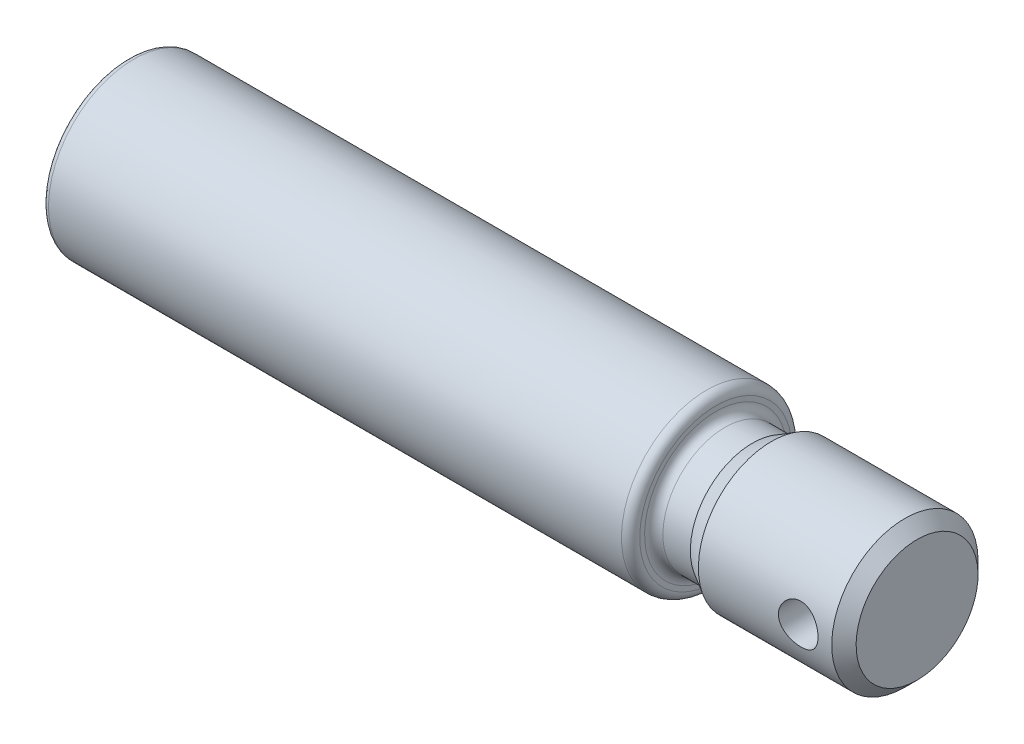
SolidWorks part; units mm, degrees
ref_plane "Plane1" through (0, 0, 0) normal (0, 0, 1) x (1, 0, 0)
ref_plane "Plane2" through (0, 0, 0) normal (0, 1, 0) x (1, 0, 0)
ref_plane "Plane3" through (0, 0, 0) normal (1, 0, 0) x (0, 0, -1)
sketch "Sketch1" plane through (0, 0, 0) normal (0, 0, 1) x (1, 0, 0)
  line L0 (1, 14) -> (95, 14)
  line L1 (129.5, 10) -> (127.5, 12)
  line L2 (129.5, 10) -> (129.5, 0)
  line L3 (-12.9942, 0) -> (0, 0) construction
  line L4 (0, 13) -> (0, 0)
  line L5 (0, 0) -> (129.5, 0)
  line L6 (96.5, 12.5) -> (96.5, 11.7)
  line L7 (98, 10.2) -> (102.5, 10.2)
  line L8 (102.5, 10.2) -> (105.6177, 12)
  line L9 (105.6177, 12) -> (127.5, 12)
  arc A0 (95, 14) -> (96.5, 12.5) centre (95, 12.5) cw
  arc A1 (98, 10.2) -> (96.5, 11.7) centre (98, 11.7) cw
  arc A2 (1, 14) -> (0, 13) centre (1, 13) ccw
  dimension "D10" = 1.5
  dimension "D11" = 1
  dimension "D1" = 28
  dimension "D2" = 129.5
  dimension "D3" = 27
  dimension "D4" = 33
  dimension "D5" = 24
  dimension "D6" = 20.4
  dimension "D7" = 30
  dimension "D8" = 2
  dimension "D9" = 45
revolve "Base-Revolve" add sketch "Sketch1" angle 360 about L3
cosmetic thread "Cosmetic Thread1" parameters "D2"=26.211
sketch "Sketch2" plane through (0, 0, 0) normal (0, 0, 1) x (1, 0, 0)
  line L0 (0, 0) -> (195, 0) construction
  line L1 (0, 0) -> (-12.9942, 0) construction
  line L2 (129.5, -10) -> (129.5, 10) construction
  circle A0 centre (122, 0) radius 3.25
  dimension "D1" = 6.5
  dimension "D2" = 7.5
extrude "ø6.5 hul" cut sketch "Sketch2" against normal mid plane 50
